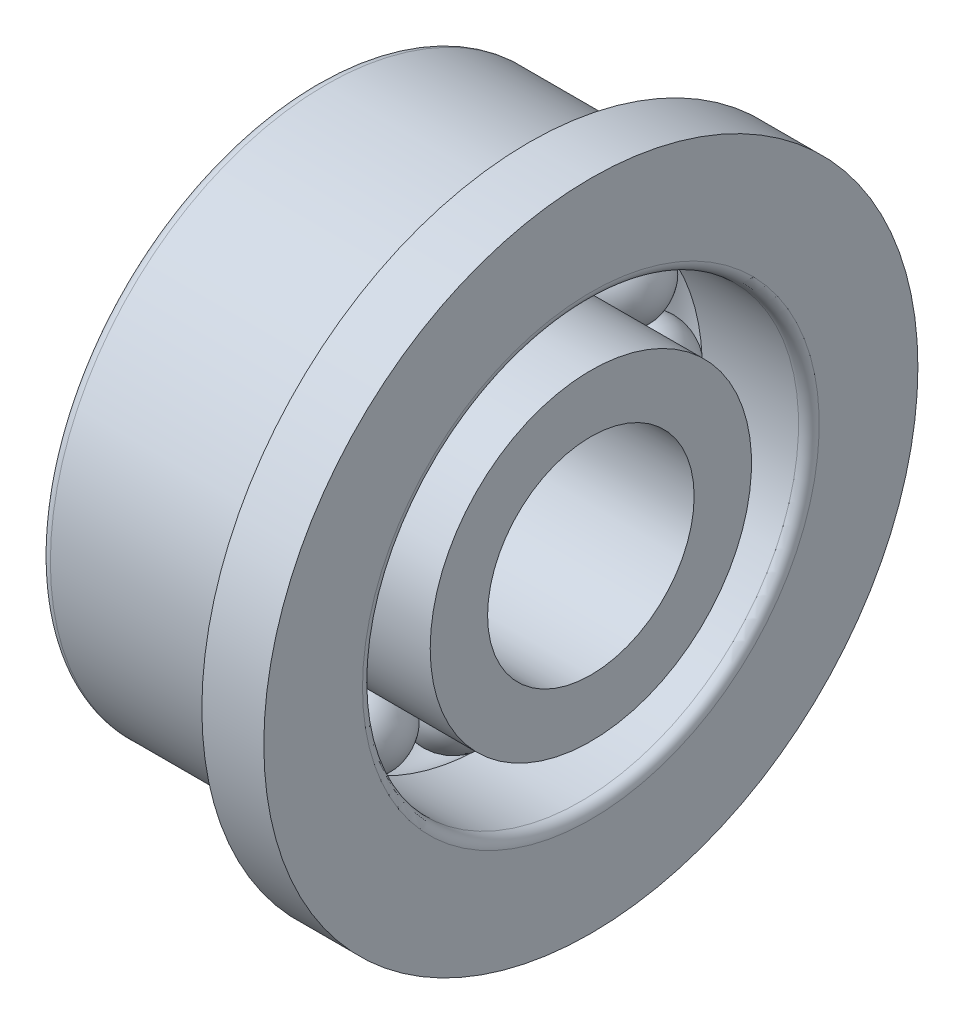
SolidWorks part; units mm, degrees
ref_plane "Front" through (0, 0, 0) normal (0, 0, 1) x (1, 0, 0)
ref_plane "Top" through (0, 0, 0) normal (0, 1, 0) x (1, 0, 0)
ref_plane "Right" through (0, 0, 0) normal (1, 0, 0) x (0, 0, -1)
sketch "Sketch1" plane through (0, 0, 0) normal (0, 0, 1) x (1, 0, 0)
  line L0 (-0.8071, 0) -> (0.9386, 0) construction
  line L1 (-0.8071, 2.75) -> (0.9386, 2.75) construction
  line L2 (-0.625, 2.75) -> (0.625, 2.75)
  arc A0 (-0.625, 2.75) -> (0.625, 2.75) centre (0, 2.75) ccw
  dimension "D2" = 1.25
  dimension "D1" = 2.75
revolve "Revolve1" add sketch "Sketch1" angle 360 about L1
sketch "Sketch2" plane through (0, 0, 0) normal (0, 0, 1) x (1, 0, 0)
  line L0 (-2, 2.3333) -> (-0.4523, 2.3333)
  line L1 (2, 2.3333) -> (2, 1.5)
  line L2 (2, 1.5) -> (-2, 1.5)
  line L3 (-2, 1.5) -> (-2, 2.3333)
  line L4 (-0.8417, 0) -> (1.1297, 0) construction
  line L5 (-0.8417, 2.75) -> (0.9121, 2.75) construction
  line L6 (0.4523, 2.3333) -> (2, 2.3333)
  arc A0 (-0.4523, 2.3333) -> (0.4523, 2.3333) centre (0, 2.75) ccw
  dimension "D6" = 1.23
  dimension "D1" = 3
  dimension "D2" = 2.75
  dimension "D3" = 4
  dimension "D4" = 2
  dimension "D5" = 4.6667
revolve "Revolve2" add sketch "Sketch2" angle 360 about L4
sketch "Sketch3" plane through (0, 0, 0) normal (0, 0, 1) x (1, 0, 0)
  line L0 (-2, 4) -> (-2, 3.1667)
  line L1 (-2, 3.1667) -> (-0.4523, 3.1667)
  line L2 (2, 3.1667) -> (2, 4.75)
  line L3 (2, 4.75) -> (1.1, 4.75)
  line L4 (1.1, 4.75) -> (1.1, 4.0375)
  line L5 (1.0625, 4) -> (-2, 4)
  line L6 (-0.9997, 0) -> (1.1297, 0) construction
  line L8 (-0.9997, 2.75) -> (0.9355, 2.75) construction
  line L9 (0.4523, 3.1667) -> (2, 3.1667)
  arc A0 (0.4523, 3.1667) -> (-0.4523, 3.1667) centre (0, 2.75) ccw
  arc A1 (1.0625, 4) -> (1.1, 4.0375) centre (1.1, 4) ccw
  dimension "D8" = 1.23
  dimension "D1" = 0.075
  dimension "R" = 2.75
  dimension "DD" = 8
  dimension "DD1" = 9.5
  dimension "C1" = 0.9
  dimension "B" = 4
  dimension "D6" = 2
  dimension "D7" = 6.3333
revolve "Revolve3" add sketch "Sketch3" angle 360 about L6
pattern_circular "Circular-Pattern1" count 12 over 360 about axis through (0, 0, 0) along (1, 0, 0) of "Revolve1"
fillet "Fillet1" radius 0.15 3 edges at (2, 0, 3.1667) (-2, 0, 4) (-2, 0, 1.5)
equation "\"D1@Sketch1\" = ( \"DD@Sketch3\" + \"D1@Sketch2\" )  / 4"
equation "\"D2@Sketch1\" =  ( \"DD@Sketch3\" - \"D1@Sketch2\" )  / 4"
equation "\"D4@Sketch2\" = \"D3@Sketch2\" / 2"
equation "\"D5@Sketch2\" = \"D1@Sketch2\" +  ( \"DD@Sketch3\" - \"D1@Sketch2\" )  / 3"
equation "\"D2@Sketch2\" = ( \"DD@Sketch3\" + \"D1@Sketch2\" )  / 4"
equation "\"D6@Sketch2\" =  ( \"DD@Sketch3\" - \"D1@Sketch2\" )  / 4 - 0.02"
equation "\"B@Sketch3\" = \"D3@Sketch2\""
equation "\"D6@Sketch3\" = \"B@Sketch3\" / 2"
equation "\"R@Sketch3\" = ( \"DD@Sketch3\" + \"D1@Sketch2\" )  / 4"
equation "\"D7@Sketch3\" = \"DD@Sketch3\" -  ( \"DD@Sketch3\"  - \"D1@Sketch2\") / 3 "
equation "\"D8@Sketch3\" = ( \"DD@Sketch3\" - \"D1@Sketch2\" )  / 4 - 0.02"
equation "\"m@Circular-Pattern1\" = int( 3.14159265 / atn((\"D2@Sketch1\"/2) / sqr(( \"DD@Sketch3\" + \"D1@Sketch2\" )  / 4 * ( \"DD@Sketch3\" + \"D1@Sketch2\" )  / 4 - (\"D2@Sketch1\"/2) *  (\"D2@Sketch1\"/2))))-1"
equation "\"D1@Sketch3\" =  ( \"DD1@Sketch3\" - \"DD@Sketch3\" )  / 20"
